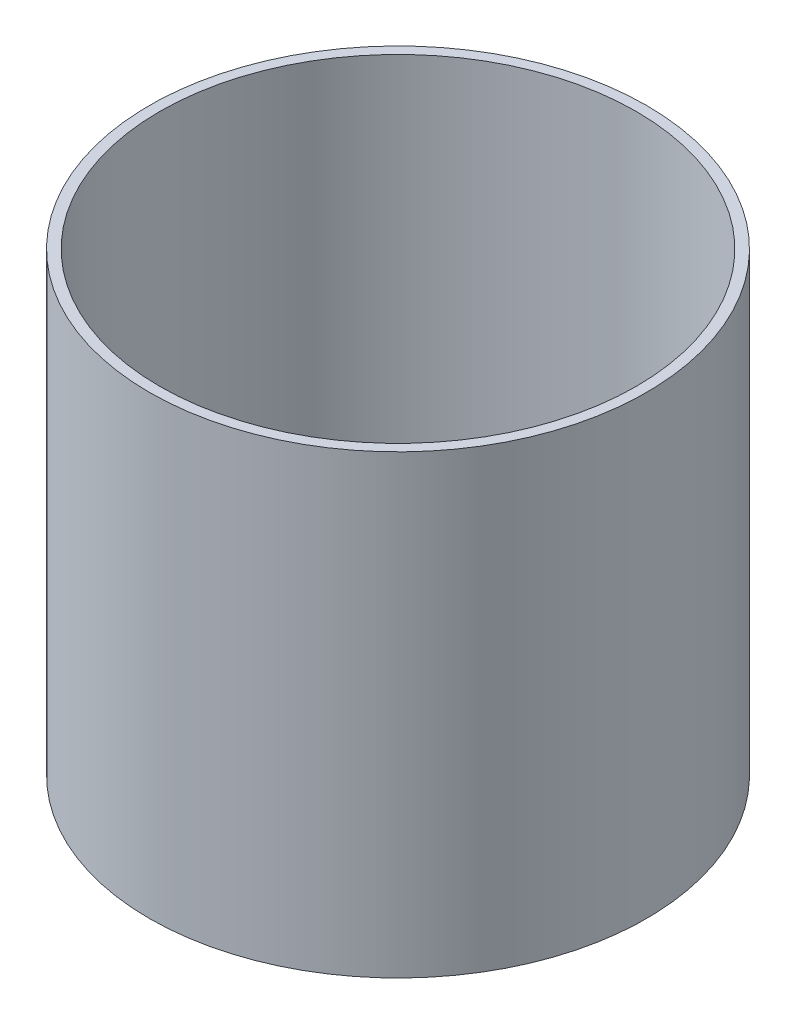
SolidWorks part; units mm, degrees
material "6061-T6"
ref_plane "Front Plane" through (0, 0, 0) normal (0, 0, 1) x (1, 0, 0)
ref_plane "Top Plane" through (0, 0, 0) normal (0, 1, 0) x (1, 0, 0)
ref_plane "Right Plane" through (0, 0, 0) normal (1, 0, 0) x (0, 0, -1)
sketch "Sketch1" plane through (0, 0, 0) normal (0, 1, 0) x (1, 0, 0)
  circle A0 centre (0, 0) radius 152.4
  circle A1 centre (0, 0) radius 146.05
  dimension "D1" = 304.8
  dimension "D2" = 6.35
extrude "Boss-Extrude1" add sketch "Sketch1" along normal blind 279.4
